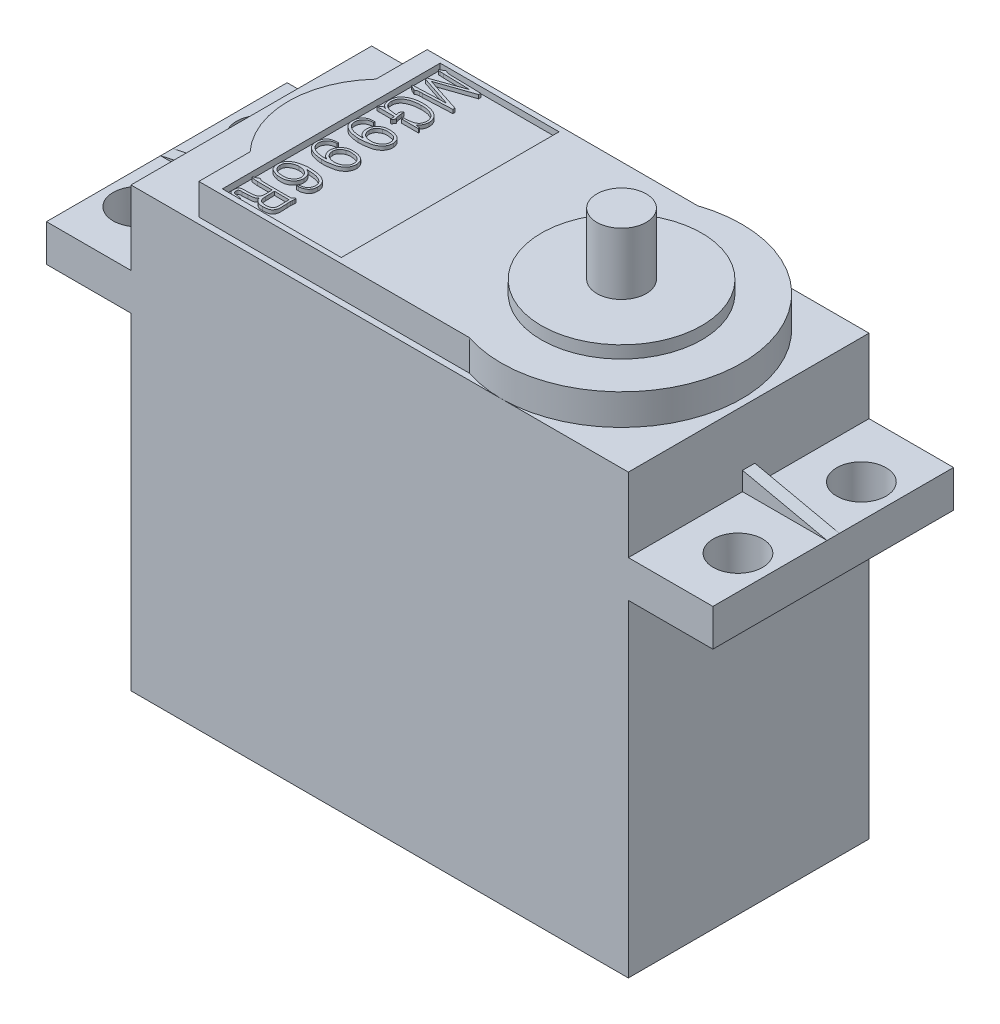
SolidWorks part; units mm, degrees
material "CA"
ref_plane "前视基准面" through (0, 0, 0) normal (0, 0, 1) x (1, 0, 0)
ref_plane "上视基准面" through (0, 0, 0) normal (0, 1, 0) x (1, 0, 0)
ref_plane "右视基准面" through (0, 0, 0) normal (1, 0, 0) x (0, 0, -1)
sketch "草图1" plane through (0, 0, 0) normal (0, 1, 0) x (1, 0, 0)
  line L1 (-20.15, 9.75) -> (20.15, 9.75)
  line L2 (-20.15, 9.75) -> (-20.15, -9.75)
  line L3 (-20.15, -9.75) -> (20.15, -9.75)
  line L4 (20.15, 9.75) -> (20.15, -9.75)
  line L5 (-20.15, 9.75) -> (20.15, -9.75) construction
  line L6 (-20.15, -9.75) -> (20.15, 9.75) construction
  point P0 (0, 0)
  dimension "D1" = 40.3
  dimension "D2" = 19.5
extrude "凸台-拉伸1" add sketch "草图1" along normal blind 28.5
sketch "草图2" plane through (0, 28.5, 0) normal (0, 1, 0) x (1, 0, 0)
  line L1 (-27, 9.75) -> (27, 9.75)
  line L2 (-27, 9.75) -> (-27, -9.75)
  line L3 (-27, -9.75) -> (27, -9.75)
  line L4 (27, 9.75) -> (27, -9.75)
  line L5 (-27, 9.75) -> (27, -9.75) construction
  line L6 (-27, -9.75) -> (27, 9.75) construction
  point P0 (0, 0)
  dimension "D1" = 54
  dimension "D2" = 19.5
extrude "凸台-拉伸2" add sketch "草图2" along normal blind 3
sketch "草图3" plane through (0, 31.5, 0) normal (0, 1, 0) x (1, 0, 0)
  line L0 (-27, -9.75) -> (27, -9.75) construction
  line L1 (-20.15, 9.75) -> (20.15, 9.75)
  line L2 (-20.15, 9.75) -> (-20.15, -9.75)
  line L3 (-20.15, -9.75) -> (20.15, -9.75)
  line L4 (20.15, 9.75) -> (20.15, -9.75)
  line L5 (-20.15, 9.75) -> (20.15, -9.75) construction
  line L6 (-20.15, -9.75) -> (20.15, 9.75) construction
  line L7 (-27, 9.75) -> (-27, -9.75) construction
  point P0 (0, 0)
  dimension "D1" = 6.85
extrude "凸台-拉伸3" add sketch "草图3" along normal blind 6
sketch "草图4" plane through (0, 37.5, 0) normal (0, 1, 0) x (1, 0, 0)
  line L0 (27, -9.75) -> (27, 9.75) construction
  line L1 (20.15, 9.75) -> (-20.15, 9.75) construction
  line L2 (-28.674, 0) -> (31.5591, 0) construction
  line L3 (-15.15, -9.25) -> (-15.15, -5.099)
  line L4 (-15.15, 9.25) -> (6.7678, 9.25)
  line L5 (-20.15, 9.75) -> (-20.15, -9.75) construction
  line L6 (-15.15, -9.25) -> (6.7678, -9.25)
  line L7 (-20.15, -9.75) -> (20.15, -9.75) construction
  line L8 (-20.15, 9.75) -> (-20.15, -9.75) construction
  line L9 (-15.15, 5.099) -> (-15.15, 9.25)
  arc A0 (6.7678, -9.25) -> (6.7678, 9.25) centre (9.85, 0) ccw
  arc A1 (-15.15, 5.099) -> (-15.15, -5.099) centre (-9.65, 0) ccw
  point P15 (-15.15, 0)
  dimension "D4" = 15
  dimension "D1" = 17.15
  dimension "D2" = 5
  dimension "D3" = 0.5
  dimension "D5" = 10.5
extrude "凸台-拉伸4" add sketch "草图4" along normal blind 2.5
ref_plane "基准面1" through (0, 0, 0) normal (0, 0, 1) x (1, 0, 0)
sketch "草图5" plane through (0, 0, 0) normal (0, 0, 1) x (1, 0, 0)
  line L2 (20.15, 33) -> (27, 31.5)
  line L3 (20.15, 37.5) -> (20.15, 31.5) construction
  line L4 (20.15, 31.5) -> (27, 31.5) construction
  line L5 (27, 31.5) -> (27, 28.5) construction
  dimension "D2" = 1.5
rib "筋1" sketch "草图5" sketch "草图5" thickness 1 extrusion direction parallel to sketch draft on no parameters "D1"=1
sketch "草图6" plane through (0, 0, 0) normal (0, 0, 1) x (1, 0, 0)
  line L0 (-20.15, 33) -> (-27, 31.5)
  line L1 (-20.15, 37.5) -> (-20.15, 31.5) construction
  dimension "D1" = 1.5
rib "筋2" sketch "草图6" sketch "草图6" thickness 1 extrusion direction parallel to sketch draft on no parameters "D1"=1
sketch "草图7" plane through (0, 40, 0) normal (0, 1, 0) x (1, 0, 0)
  circle A0 centre (9.85, 0) radius 6.5
  dimension "D1" = 13
extrude "凸台-拉伸5" add sketch "草图7" along normal blind 1
sketch "草图9" plane through (0, 31.5, 0) normal (0, 1, 0) x (1, 0, 0)
  line L0 (-32.7219, 0) -> (36.2848, 0) construction
  line L2 (-27, 9.75) -> (-27, 0.5) construction
  circle A0 centre (-24.35, 5) radius 2
  circle A1 centre (24.28, 5) radius 2
  circle A4 centre (24.28, -5) radius 2
  circle A5 centre (-24.35, -5) radius 2
  dimension "D3" = 4
  dimension "D4" = 4
  dimension "D1" = 5
  dimension "D2" = 5
  dimension "D5" = 48.63
  dimension "D6" = 2.65
extrude "切除-拉伸2" cut sketch "草图9" against normal blind 5
chamfer "倒角1" distance 2 angle 45 4 edges at (-20.15, 0, 0) (0, 0, -9.75) (20.15, 0, 0) (0, 0, 9.75)
sketch "草图10" plane through (0, 40, 0) normal (0, 1, 0) x (1, 0, 0)
  line L0 (-19.525, 0) -> (19.525, 0) construction
  line L1 (-13.673, 8.8233) -> (-4.0362, 8.8233)
  line L2 (-13.673, 8.8233) -> (-13.673, -8.8233)
  line L3 (-13.673, -8.8233) -> (-4.0362, -8.8233)
  line L4 (-4.0362, 8.8233) -> (-4.0362, -8.8233)
  line L5 (-13.673, 8.8233) -> (-4.0362, -8.8233) construction
  line L6 (-13.673, -8.8233) -> (-4.0362, 8.8233) construction
  line L7 (-27, 9.75) -> (-27, 0.5) construction
  point P0 (-8.8546, 0)
  dimension "D1" = 13.327
  dimension "D2" = 9.6368
  dimension "D3" = 17.6466
extrude "切除-拉伸3" cut sketch "草图10" against normal blind 0.5
sketch "草图11" plane through (0, 39.5, 0) normal (0, 1, 0) x (1, 0, 0)
  text T0 "MG996R" font "汉仪长仿宋体" height 3.5
extrude "凸台-拉伸6" add sketch "草图11" along normal blind 0.3
sketch "草图12" plane through (0, 41, 0) normal (0, 1, 0) x (1, 0, 0)
  circle A0 centre (9.85, 0) radius 2
extrude "凸台-拉伸7" add sketch "草图12" along normal blind 5 contours A0
